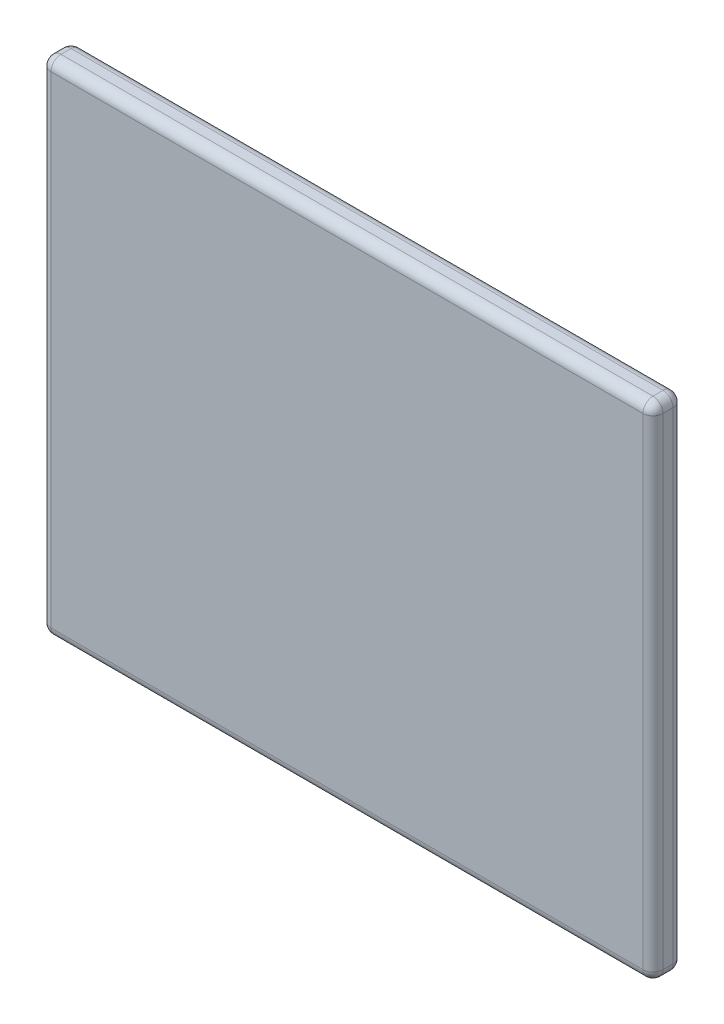
SolidWorks part; units mm, degrees
ref_plane "前视基准面" through (0, 0, 0) normal (0, 0, 1) x (1, 0, 0)
ref_plane "上视基准面" through (0, 0, 0) normal (0, 1, 0) x (1, 0, 0)
ref_plane "右视基准面" through (0, 0, 0) normal (1, 0, 0) x (0, 0, -1)
sketch "草图1" plane through (0, 0, 0) normal (0, 0, 1) x (1, 0, 0)
  line L1 (-30.5, 25) -> (30.5, 25)
  line L2 (-30.5, 25) -> (-30.5, -25)
  line L3 (-30.5, -25) -> (30.5, -25)
  line L4 (30.5, 25) -> (30.5, -25)
  line L5 (-30.5, 25) -> (30.5, -25) construction
  line L6 (-30.5, -25) -> (30.5, 25) construction
  point P0 (0, 0)
  dimension "D1" = 61
  dimension "D2" = 50
extrude "凸台-拉伸1" add sketch "草图1" along normal blind 3
fillet "圆角1" radius 1 12 edges at (0, 25, 3) (0, 25, 0) (30.5, 0, 3) (30.5, 25, 1.5) (30.5, 0, 0) (0, -25, 3) (30.5, -25, 1.5) (0, -25, 0) (-30.5, 25, 1.5) (-30.5, 0, 3) (-30.5, -25, 1.5) (-30.5, 0, 0)
